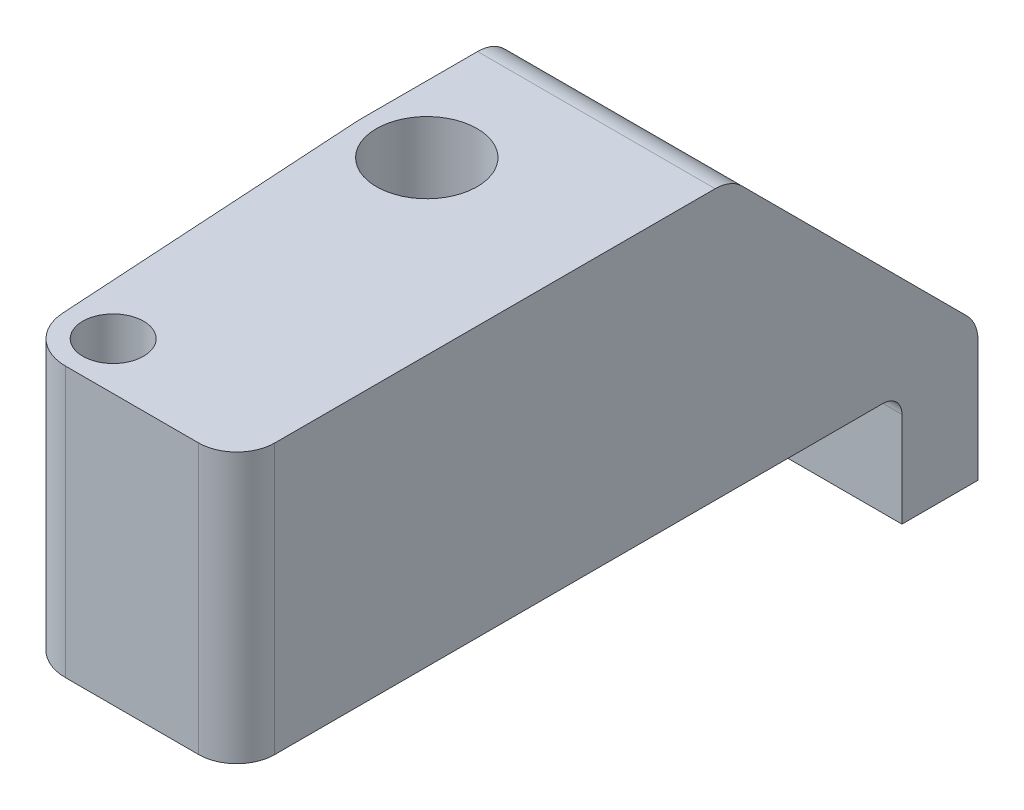
SolidWorks part; units mm, degrees
ref_plane "Front Plane" through (0, 0, 0) normal (0, 0, 1) x (1, 0, 0)
ref_plane "Top Plane" through (0, 0, 0) normal (0, 1, 0) x (1, 0, 0)
ref_plane "Right Plane" through (0, 0, 0) normal (1, 0, 0) x (0, 0, -1)
sketch "Sketch1" plane through (0, 0, 0) normal (0, 1, 0) x (1, 0, 0)
  line L0 (0, 0) -> (0, 37.1567) construction
  line L1 (0, 0) -> (0, -6) construction
  line L2 (-8.5175, 32.5) -> (8.5175, 32.5) construction
  line L3 (-7.767, -6) -> (7.767, -6) construction
  line L4 (-3.4936, 16.2879) -> (-2.4954, -0.1515)
  line L5 (-3.5, 16.5) -> (3.5, 16.5)
  line L6 (-3.5, 16.5) -> (-3.5, 32.5)
  line L7 (-3.5, 32.5) -> (3.5, 32.5)
  line L8 (3.5, 16.5) -> (3.5, 32.5)
  line L9 (3.4936, 16.2879) -> (2.4954, -0.1515)
  line L11 (0, -2.5) -> (9, -2.5)
  line L12 (0, -2.5) -> (0, 32.5)
  line L13 (0, 32.5) -> (9, 32.5)
  line L14 (9, -2.5) -> (9, 32.5)
  arc A0 (-2.4954, -0.1515) -> (2.4954, -0.1515) centre (0, 0) ccw
  arc A1 (3.4936, 16.2879) -> (3.5, 16.5) centre (0, 16.5) ccw
  arc A2 (-3.5, 16.5) -> (-3.4936, 16.2879) centre (0, 16.5) ccw
  point P11 (0, 32.5)
  point P12 (0, -6)
  dimension "D1" = 16.5
  dimension "D2" = 7
  dimension "D5" = 2.5
  dimension "D3" = 6
  dimension "D4" = 16
  dimension "D6" = 9
extrude "Boss-Extrude1" add sketch "Sketch1" along normal blind 14.2 contours L5 A2 L4 A0 L9 A1 | L5 L8 L7 L6 | A1 L9 A0 L11 L14 L13 L8 | L9 A1 L5 L12 A0 | L12 L5 L8 L7
hole_wizard "M3 Clearance Hole1" positions "Sketch2" profile "Sketch3" hole size "M3" standard "ANSI Metric" end condition through all
sketch "Sketch2" plane through (0, 0, 0) normal (0, -1, 0) x (-1, 0, 0)
  point P0 (0, 0)
sketch "Sketch3" plane through (0, 0, 0) normal (1, 0, 0) x (0, 0, -1)
  line L0 (0, 0) -> (0, 14.2)
  line L1 (0, 14.2) -> (1.6, 14.2)
  line L2 (1.6, 14.2) -> (1.6, 0)
  line L5 (1.6, 0) -> (0, 0)
  line L11 (0, -6.35) -> (0, 107.95) construction
  dimension "Thru Hole Dia." = 3.2
  dimension "Thru Hole Depth" = 14.2
hole_wizard "M5 Clearance Hole1" positions "Sketch4" profile "Sketch5" hole size "M5" standard "ANSI Metric" end condition through all
sketch "Sketch4" plane through (0, 0, 0) normal (0, -1, 0) x (-1, 0, 0)
  point P0 (0, 16.5)
sketch "Sketch5" plane through (0, 0, -16.5) normal (1, 0, 0) x (0, 0, -1)
  line L0 (0, 0) -> (0, 14.2)
  line L1 (0, 14.2) -> (2.65, 14.2)
  line L2 (2.65, 14.2) -> (2.65, 0)
  line L5 (2.65, 0) -> (0, 0)
  line L11 (0, -6.35) -> (0, 107.95) construction
  dimension "Thru Hole Dia." = 5.3
  dimension "Thru Hole Depth" = 14.2
sketch "Sketch6" plane through (0, 0, 0) normal (0, -1, 0) x (1, 0, 0)
  line L1 (9, -32.5) -> (-5.6325, -32.5)
  line L2 (9, -32.5) -> (9, -36.5)
  line L3 (9, -36.5) -> (-5.6325, -36.5)
  line L4 (-5.6325, -32.5) -> (-5.6325, -36.5)
  point P4 (0, 0)
  point P5 (0, 0)
  point P6 (-5.6325, -32.5)
  dimension "D1" = 4
extrude "Boss-Extrude2" add sketch "Sketch6" along normal blind 6 and the other way up to surface (14.2 mm away) other way up to face at (0, 14.2, -19.15)
fillet "Fillet1" radius 1 1 edges at (2.75, 0, -32.5)
fillet "Fillet2" radius 2 1 edges at (9, 7.1, 2.5)
sketch "Sketch7" plane through (0, 0, 0) normal (0, -1, 0) x (1, 0, 0)
  line L0 (-3.5, -16.5) -> (-3.5, -31.5) construction
  line L1 (-3.5, -29.7062) -> (-12.0697, -29.7062)
  line L2 (-3.5, -29.7062) -> (-3.5, -43.2203)
  line L3 (-3.5, -43.2203) -> (-12.0697, -43.2203)
  line L4 (-12.0697, -29.7062) -> (-12.0697, -43.2203)
extrude "Cut-Extrude1" cut sketch "Sketch7" against normal blind 10
chamfer "Chamfer1" distance 13 1 edges at (1.6838, 14.2, -36.5)
fillet "Fillet4" radius 2 2 edges at (2.75, 14.2, -23.5) (2.75, 1.2, -36.5)
